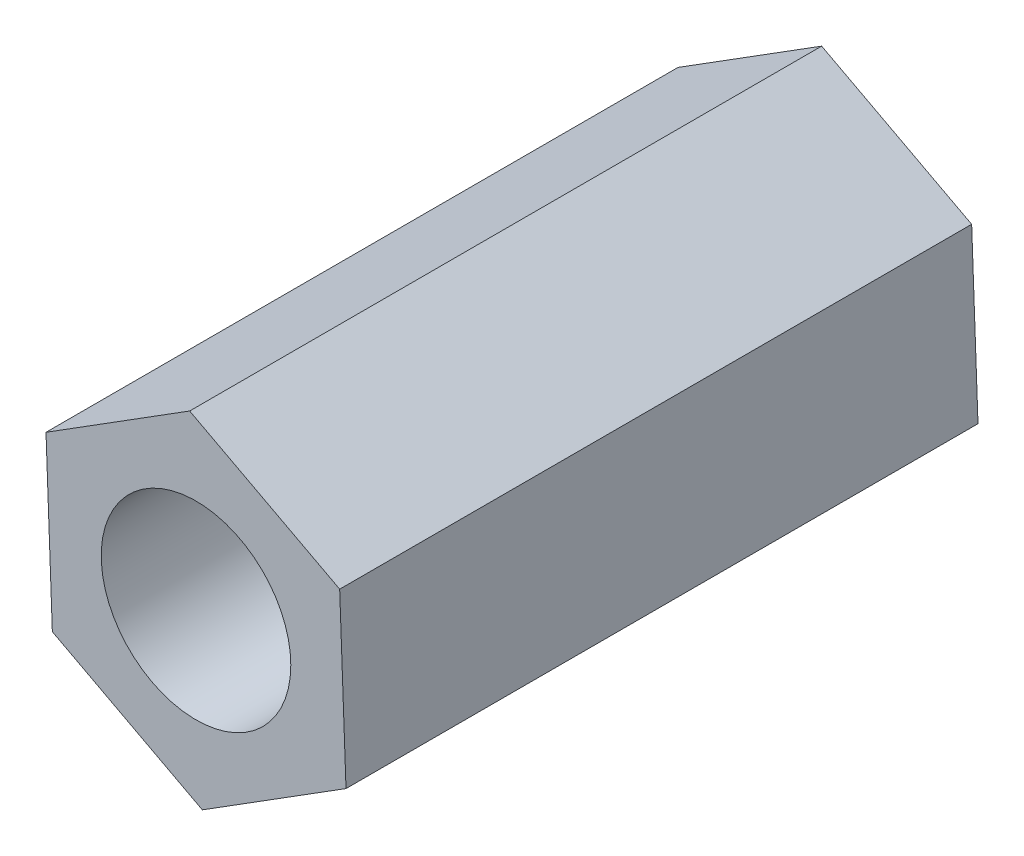
SolidWorks part; units mm, degrees
ref_plane "前视基准面" through (0, 0, 0) normal (0, 0, 1) x (1, 0, 0)
ref_plane "上视基准面" through (0, 0, 0) normal (0, 1, 0) x (1, 0, 0)
ref_plane "右视基准面" through (0, 0, 0) normal (1, 0, 0) x (0, 0, -1)
sketch "草图1" plane through (0, 0, 0) normal (0, 0, 1) x (1, 0, 0)
  line L1 (2.2732, 1.4283) -> (-0.1003, 2.6828)
  line L2 (-0.1003, 2.6828) -> (-2.3735, 1.2545)
  line L3 (-2.3735, 1.2545) -> (-2.2732, -1.4283)
  line L4 (-2.2732, -1.4283) -> (0.1003, -2.6828)
  line L5 (0.1003, -2.6828) -> (2.3735, -1.2545)
  line L6 (2.3735, -1.2545) -> (2.2732, 1.4283)
  circle A0 centre (0, 0) radius 2.325 construction
  circle A1 centre (0, 0) radius 1.5
extrude "凸台-拉伸1" add sketch "草图1" along normal blind 10
